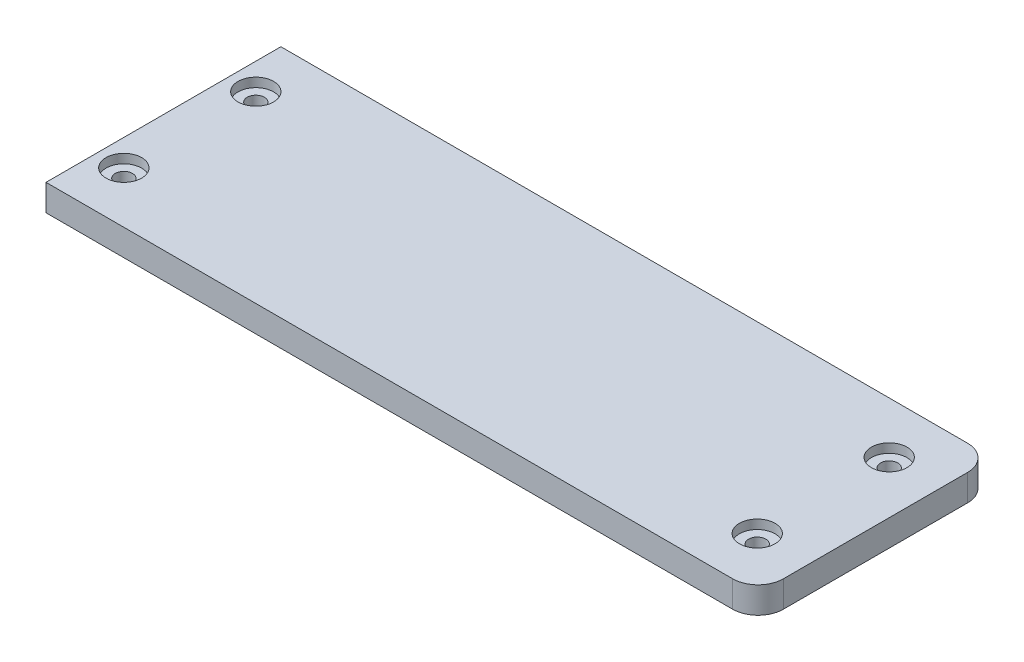
SolidWorks part; units mm, degrees
ref_plane "Front Plane" through (0, 0, 0) normal (0, 0, 1) x (1, 0, 0)
ref_plane "Top Plane" through (0, 0, 0) normal (0, 1, 0) x (1, 0, 0)
ref_plane "Right Plane" through (0, 0, 0) normal (1, 0, 0) x (0, 0, -1)
sketch "Sketch1" plane through (0, 0, 0) normal (0, 1, 0) x (1, 0, 0)
  line L1 (-66.27, 28.7689) -> (63.73, 28.7689)
  line L2 (-66.27, 28.7689) -> (-66.27, -15.7311)
  line L3 (-66.27, -15.7311) -> (63.73, -15.7311)
  line L4 (63.73, 28.7689) -> (63.73, -15.7311)
  dimension "D1" = 130
  dimension "D2" = 44.5
extrude "Boss-Extrude1" add sketch "Sketch1" along normal blind 5
sketch "Sketch2" plane through (0, 5, 0) normal (0, 1, 0) x (1, 0, 0)
  line L0 (-66.27, -15.7311) -> (63.73, -15.7311) construction
  line L1 (58.73, -5.9811) -> (-61.27, -5.9811)
  line L2 (58.73, -5.9811) -> (58.73, 19.0189)
  line L3 (58.73, 19.0189) -> (-61.27, 19.0189)
  line L4 (-61.27, -5.9811) -> (-61.27, 19.0189)
  line L5 (63.73, -15.7311) -> (63.73, 28.7689) construction
  point P6 (63.73, 6.5189)
  point P7 (58.73, 6.5189)
  point P10 (-1.27, -5.9811)
  point P11 (-1.27, -15.7311)
  dimension "D1" = 0
  dimension "D2" = 0
  dimension "D3" = 25
  dimension "D4" = 120
hole_wizard "CBORE for #4 Binding Head Machine Screw1" positions "Sketch3" profile "Sketch4" counterbore size "#4" standard "ANSI Inch" end condition up to next
sketch "Sketch3" plane through (0, 5, 0) normal (0, 1, 0) x (1, 0, 0)
  point P0 (-61.27, 19.0189)
  point P3 (-61.27, -5.9811)
  point P6 (58.73, -5.9811)
  point P9 (58.73, 19.0189)
sketch "Sketch4" plane through (-61.27, 5, -19.0189) normal (1, 0, 0) x (0, 0, 1)
  line L0 (0, 0) -> (0, 5)
  line L1 (0, 5) -> (1.6319, 5)
  line L3 (1.6319, 5) -> (1.632, 1.7272)
  line L4 (1.632, 1.7272) -> (3.3731, 1.7272)
  line L5 (3.3731, 1.7272) -> (3.3731, 0)
  line L7 (3.3731, 0) -> (0, 0)
  line L11 (0, -6.35) -> (0, 107.95) construction
  dimension "Thru Hole Dia." = 3.2639
  dimension "Thru Hole Depth" = 5
  dimension "C'Bore Dia." = 6.7462
  dimension "C'Bore Depth" = 1.7272
sketch "Sketch6" plane through (0, 5, 0) normal (0, 1, 0) x (1, 0, 0)
  line L1 (63.73, 28.7689) -> (63.83, 28.7689)
  line L2 (63.73, 28.7689) -> (63.73, -15.7311)
  line L3 (63.73, -15.7311) -> (63.83, -15.7311)
  line L4 (68.63, 23.9689) -> (68.63, -10.9311)
  arc A0 (63.83, -15.7311) -> (68.63, -10.9311) centre (63.83, -10.9311) ccw
  arc A1 (63.83, 28.7689) -> (68.63, 23.9689) centre (63.83, 23.9689) cw
  point P9 (68.63, 28.7689)
  dimension "D2" = 4.8
  dimension "D1" = 4.9
extrude "Boss-Extrude2" add sketch "Sketch6" against normal blind 5
